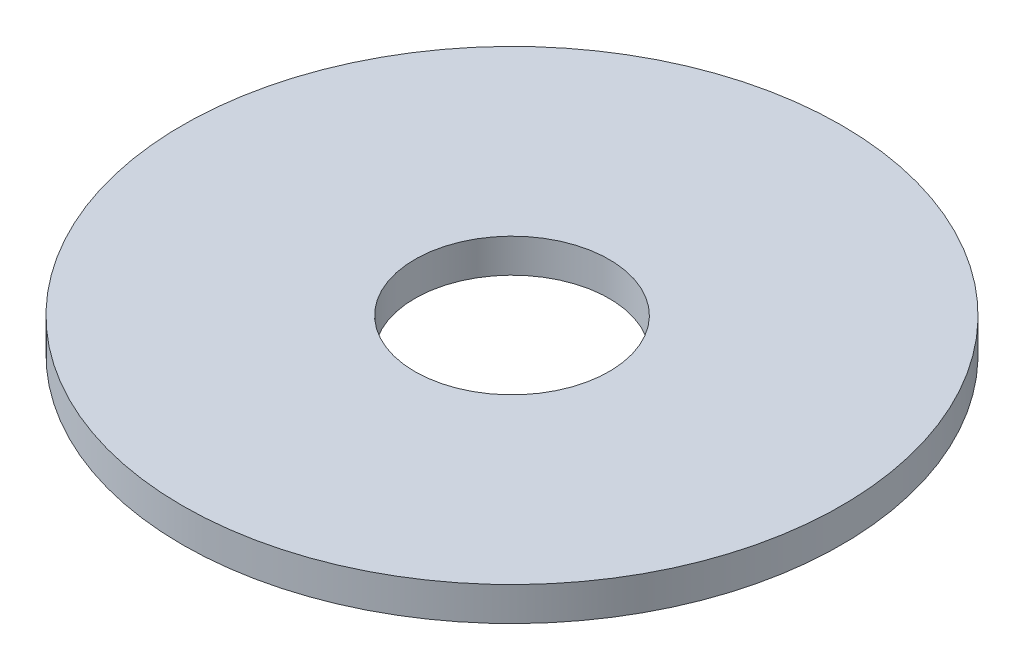
SolidWorks part; units mm, degrees
ref_plane "Front Plane" through (0, 0, 0) normal (0, 0, 1) x (1, 0, 0)
ref_plane "Top Plane" through (0, 0, 0) normal (0, 1, 0) x (1, 0, 0)
ref_plane "Right Plane" through (0, 0, 0) normal (1, 0, 0) x (0, 0, -1)
sketch "Sketch1" plane through (0, 0, 0) normal (0, 1, 0) x (1, 0, 0)
  circle A0 centre (0, 0) radius 19.5
  circle A1 centre (0, 0) radius 5.75
  dimension "D1" = 39
  dimension "D2" = 11.5
extrude "Boss-Extrude1" add sketch "Sketch1" along normal blind 2
